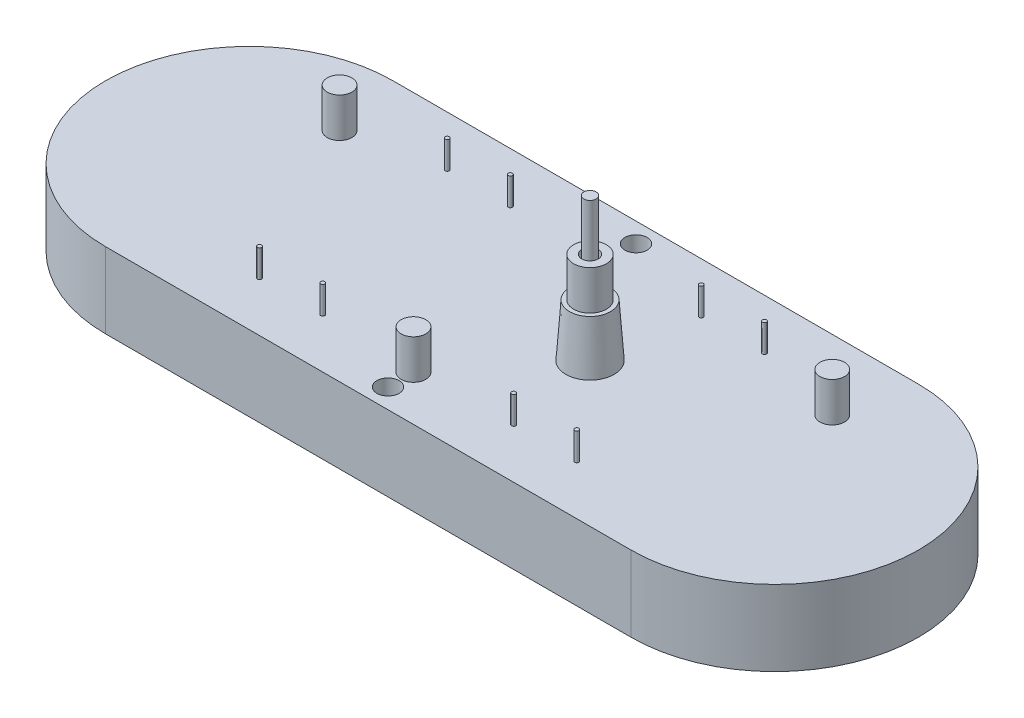
SolidWorks part; units mm, degrees
material "PET"
ref_plane "Front Plane" through (0, 0, 0) normal (0, 0, 1) x (1, 0, 0)
ref_plane "Top Plane" through (0, 0, 0) normal (0, 1, 0) x (1, 0, 0)
ref_plane "Right Plane" through (0, 0, 0) normal (1, 0, 0) x (0, 0, -1)
sketch "Sketch1" plane through (0, 0, 0) normal (0, 1, 0) x (1, 0, 0)
  line L0 (-32, 0) -> (32, 0) construction
  line L1 (-32, 17.5) -> (32, 17.5)
  line L2 (-32, -17.5) -> (32, -17.5)
  arc A0 (-32, 17.5) -> (-32, -17.5) centre (-32, 0) ccw
  arc A1 (32, -17.5) -> (32, 17.5) centre (32, 0) ccw
  point P2 (0, 0)
  dimension "D2" = 64
  dimension "D1" = 35
extrude "Boss-Extrude1" add sketch "Sketch1" against normal blind 9.2
ref_plane "Plane1" through (9.5, 0, 0) normal (1, 0, 0) x (0, 0, -1)
sketch "Sketch2" plane through (9.5, 0, 0) normal (1, 0, 0) x (0, 0, -1)
  line L0 (0, 0) -> (0, 17.4)
  line L1 (0, 17.4) -> (0.75, 17.4)
  line L2 (0.75, 17.4) -> (0.75, 0)
  line L3 (17.5, 0) -> (-17.5, 0) construction
  line L4 (0.75, 0) -> (0, 0)
  line L5 (1, 0) -> (2.9475, 0)
  line L6 (2.9475, 0) -> (2.5, 6.4)
  line L7 (2.5, 6.4) -> (2, 6.4)
  line L8 (2, 6.4) -> (2, 11.2)
  line L9 (2, 11.2) -> (1, 11.2)
  line L10 (1, 11.2) -> (1, 0)
  dimension "D1" = 17.4
  dimension "D2" = 0.75
  dimension "D3" = 4
  dimension "D4" = 1
  dimension "D5" = 11.2
  dimension "D6" = 4.8
  dimension "D7" = 2.5
  dimension "D8" = 2
revolve "Revolve1" add sketch "Sketch2" angle 360 about L0
sketch "Sketch3" plane through (0, 0, 0) normal (0, 1, 0) x (1, 0, 0)
  line L0 (0, 0) -> (0, -12) construction
  circle A0 centre (0, -12) radius 1.5
  circle A1 centre (30, 9) radius 1.5
  circle A2 centre (-30, 9) radius 1.5
  dimension "D2" = 3
  dimension "D4" = 30
  dimension "D1" = 12
  dimension "D3" = 9
extrude "Boss-Extrude2" add sketch "Sketch3" along normal blind 4.8
sketch "Sketch4" plane through (0, 0, 0) normal (0, 1, 0) x (1, 0, 0)
  line L0 (-19.32, 11.425) -> (-11.62, 11.425) construction
  line L1 (-19.32, 11.425) -> (-19.32, -11.425) construction
  line L2 (0, 0) -> (0, 17.5) construction
  line L3 (32, 17.5) -> (-32, 17.5) construction
  line L4 (19.32, 11.425) -> (19.32, -11.425) construction
  line L5 (19.32, 11.425) -> (11.62, 11.425) construction
  circle A0 centre (-19.32, 11.425) radius 0.25
  circle A1 centre (-11.62, 11.425) radius 0.25
  circle A2 centre (-11.62, -11.425) radius 0.25
  circle A3 centre (-19.32, -11.425) radius 0.25
  circle A4 centre (19.32, -11.425) radius 0.25
  circle A5 centre (11.62, -11.425) radius 0.25
  circle A6 centre (11.62, 11.425) radius 0.25
  circle A7 centre (19.32, 11.425) radius 0.25
  point P2 (-19.32, 0)
  dimension "D1" = 0.5
  dimension "D6" = 11.62
  dimension "D4" = 7.7
  dimension "D5" = 22.85
  dimension "D2" = 2
  dimension "D3" = 2
extrude "Boss-Extrude3" add sketch "Sketch4" along normal blind 3.35
sketch "Sketch5" plane through (0, 0, 0) normal (0, 1, 0) x (1, 0, 0)
  circle A0 centre (0, 15.1) radius 1.35
  circle A1 centre (0, -15.1) radius 1.35
  dimension "D1" = 2.7
  dimension "D2" = 30.2
  dimension "D3" = 15.1
extrude "Cut-Extrude1" cut sketch "Sketch5" against normal through all
